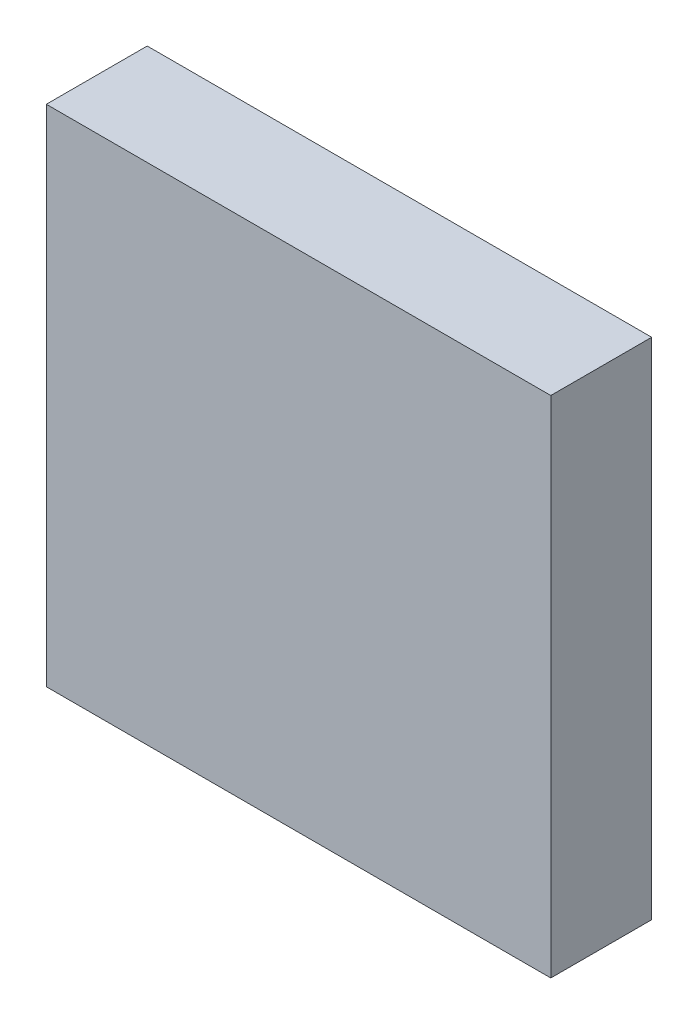
SolidWorks part; units mm, degrees
ref_plane "Спереди" through (0, 0, 0) normal (0, 0, 1) x (1, 0, 0)
ref_plane "Сверху" through (0, 0, 0) normal (0, 1, 0) x (1, 0, 0)
ref_plane "Справа" through (0, 0, 0) normal (1, 0, 0) x (0, 0, -1)
sketch "Эскиз1" plane through (0, 0, 0) normal (0, 0, 1) x (1, 0, 0)
  line L1 (-10, 10) -> (10, 10)
  line L2 (-10, 10) -> (-10, -10)
  line L3 (-10, -10) -> (10, -10)
  line L4 (10, 10) -> (10, -10)
  line L5 (-10, 10) -> (10, -10) construction
  line L6 (-10, -10) -> (10, 10) construction
  point P0 (0, 0)
  dimension "D1" = 20
  dimension "D2" = 20
extrude "Бобышка-Вытянуть1" add sketch "Эскиз1" along normal blind 4
